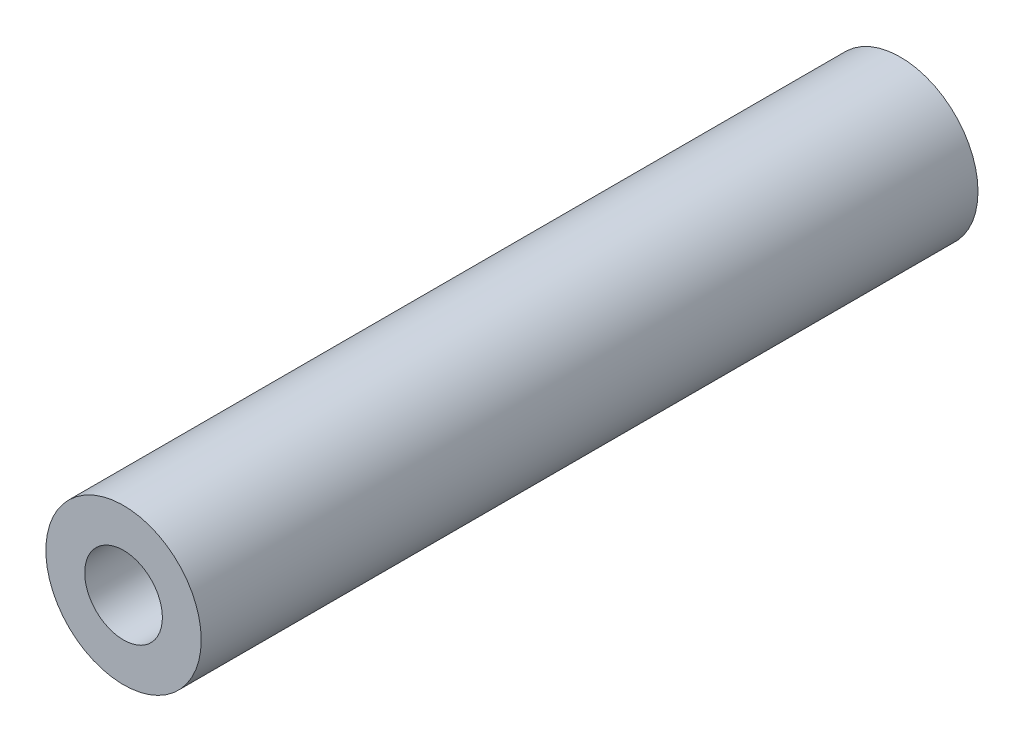
SolidWorks part; units mm, degrees
ref_plane "Piano frontale" through (0, 0, 0) normal (0, 0, 1) x (1, 0, 0)
ref_plane "Piano superiore" through (0, 0, 0) normal (0, 1, 0) x (1, 0, 0)
ref_plane "Piano destro" through (0, 0, 0) normal (1, 0, 0) x (0, 0, -1)
sketch "Schizzo1" plane through (0, 0, 0) normal (0, 0, 1) x (1, 0, 0)
  circle A0 centre (0, 0) radius 2
  circle A1 centre (0, 0) radius 1
  dimension "D1" = 2
  dimension "D2" = 4
extrude "Estrusione-Estrusione1" add sketch "Schizzo1" along normal blind 20
